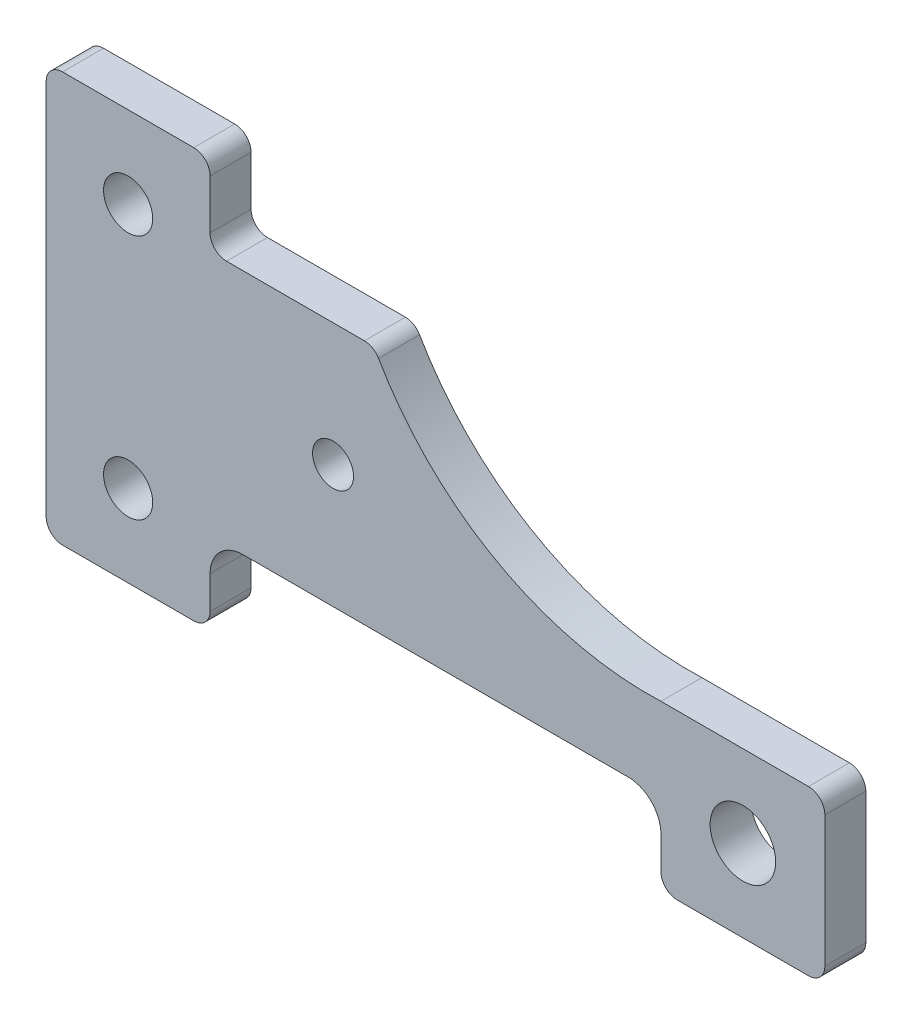
SolidWorks part; units mm, degrees
ref_plane "Ön Düzlem" through (0, 0, 0) normal (0, 0, 1) x (1, 0, 0)
ref_plane "Üst Düzlem" through (0, 0, 0) normal (0, 1, 0) x (1, 0, 0)
ref_plane "Sağ Düzlem" through (0, 0, 0) normal (1, 0, 0) x (0, 0, -1)
sketch "Çizim1" plane through (0, 0, 0) normal (0, 0, 1) x (1, 0, 0)
  line L0 (200, 20) -> (200, 60)
  line L1 (20, 0) -> (180, 0)
  line L2 (0, 20) -> (0, 480)
  line L3 (20, 500) -> (180, 500)
  line L4 (950, 20) -> (950, 180)
  line L5 (240, 100) -> (710, 100)
  line L6 (750, 60) -> (750, 20)
  line L7 (770, 0) -> (930, 0)
  line L8 (200, 480) -> (200, 420)
  line L9 (220, 400) -> (388.2419, 400)
  line L10 (930, 200) -> (750, 200)
  arc A0 (950, 180) -> (930, 200) centre (930, 180) ccw
  arc A1 (200, 420) -> (220, 400) centre (220, 420) ccw
  arc A2 (930, 0) -> (950, 20) centre (930, 20) ccw
  arc A3 (750, 20) -> (770, 0) centre (770, 20) ccw
  arc A4 (200, 20) -> (180, 0) centre (180, 20) cw
  arc A5 (20, 0) -> (0, 20) centre (20, 20) cw
  arc A6 (0, 480) -> (20, 500) centre (20, 480) cw
  arc A7 (710, 100) -> (750, 60) centre (710, 60) cw
  arc A8 (200, 60) -> (240, 100) centre (240, 60) cw
  arc A9 (200, 480) -> (180, 500) centre (180, 480) ccw
  arc A10 (405.5711, 389.9848) -> (750, 200) centre (734.8268, 579.697) ccw
  arc A11 (388.2419, 400) -> (405.5711, 389.9848) centre (388.2419, 380) cw
  circle A12 centre (100, 400) radius 30
  circle A13 centre (100, 100) radius 30
  circle A14 centre (350, 250) radius 25
  circle A15 centre (850, 100) radius 40
  point P15 (950, 200)
  point P16 (400, 400)
  point P19 (200, 400)
  point P22 (950, 0)
  point P25 (750, 0)
  point P28 (200, 0)
  point P31 (0, 0)
  point P34 (0, 500)
  point P39 (200, 100)
  point P41 (200, 500)
  point P44 (950, 200)
  point P47 (400, 400)
  point P54 (200, 450)
  point P57 (0, 0)
  point P58 (950, 100)
  dimension "D9" = 400
  dimension "D10" = 20
  dimension "D11" = 40
  dimension "D12" = 20
  dimension "D13" = 20
  dimension "D14" = 200
  dimension "D15" = 20
  dimension "D16" = 380
  dimension "D17" = 20
  dimension "D18" = 60
  dimension "D19" = 100
  dimension "D20" = 60
  dimension "D21" = 300
  dimension "D22" = 100
  dimension "D23" = 100
  dimension "D24" = 50
  dimension "D25" = 150
  dimension "D26" = 150
  dimension "D27" = 80
  dimension "D29" = 100
  dimension "D1" = 950
  dimension "D2" = 500
  dimension "D3" = 200
  dimension "D4" = 200
  dimension "D5" = 100
  dimension "D6" = 100
  dimension "D7" = 200
  dimension "D8" = 200
  dimension "D28" = 100
extrude "Yükseklik-Ekstrüzyon1" add sketch "Çizim1" along normal blind 50
